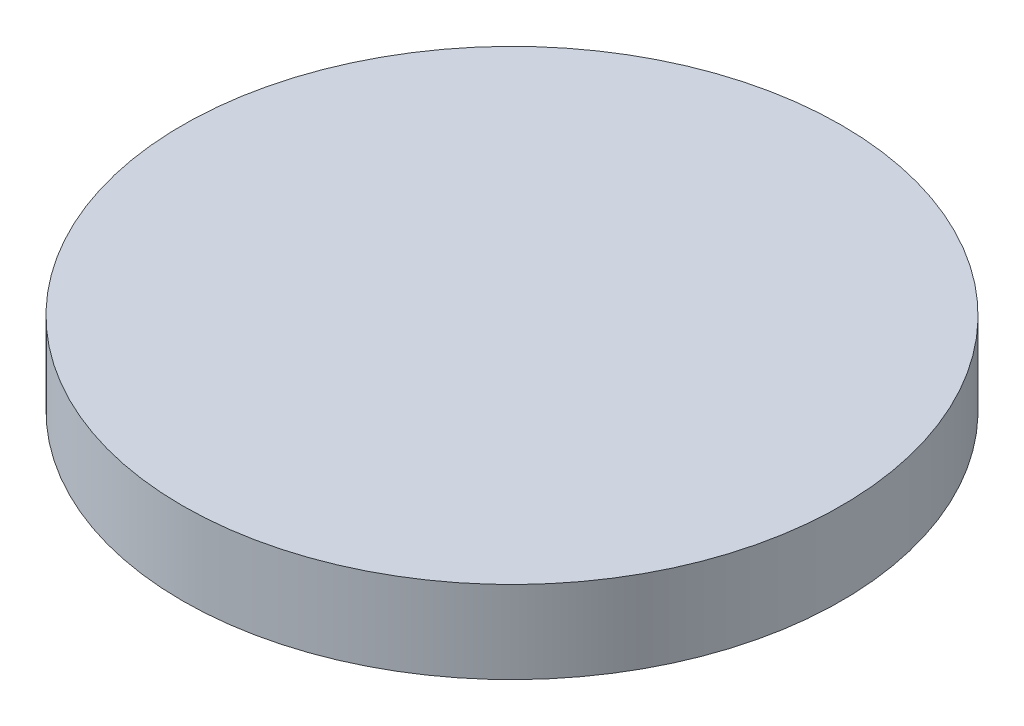
SolidWorks part; units mm, degrees
ref_plane "Front Plane" through (0, 0, 0) normal (0, 0, 1) x (1, 0, 0)
ref_plane "Top Plane" through (0, 0, 0) normal (0, 1, 0) x (1, 0, 0)
ref_plane "Right Plane" through (0, 0, 0) normal (1, 0, 0) x (0, 0, -1)
sketch "Sketch1" plane through (0, 0, 0) normal (0, 1, 0) x (1, 0, 0)
  circle A0 centre (0, 0) radius 12.7
  dimension "D1" = 25.4
extrude "Boss-Extrude1" add sketch "Sketch1" along normal blind 3.175
